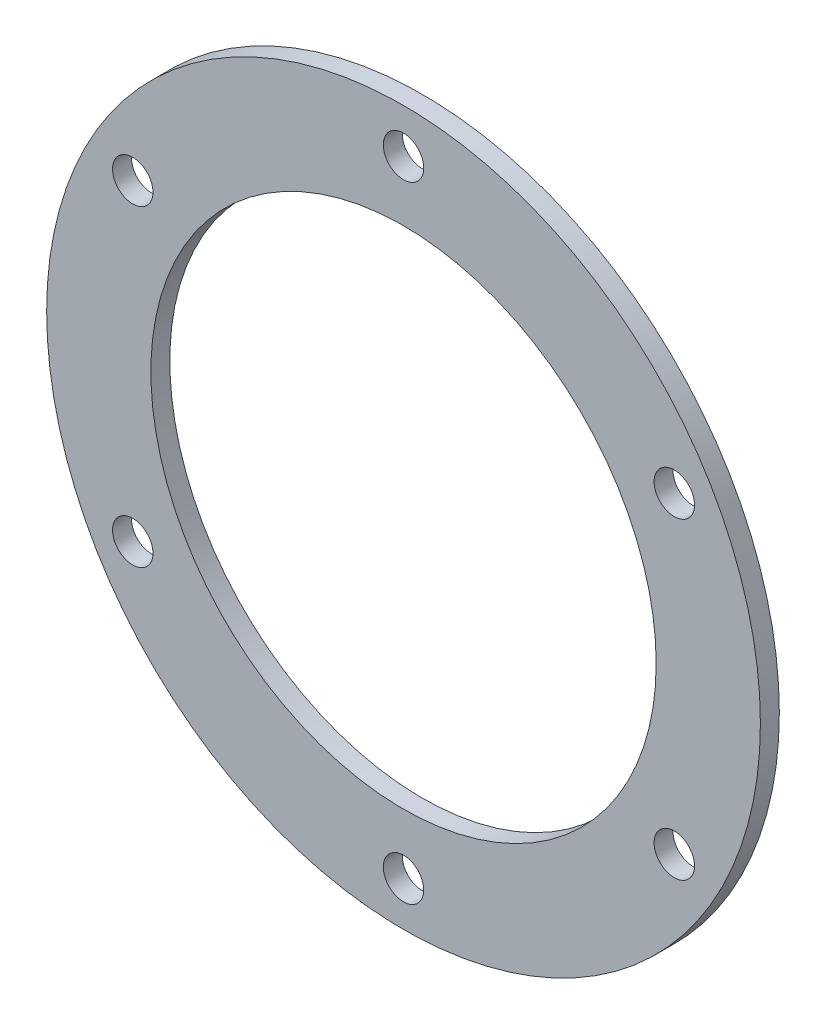
SolidWorks part; units mm, degrees
material "ABS"
ref_plane "前视基准面" through (0, 0, 0) normal (0, 0, 1) x (1, 0, 0)
ref_plane "上视基准面" through (0, 0, 0) normal (0, 1, 0) x (1, 0, 0)
ref_plane "右视基准面" through (0, 0, 0) normal (1, 0, 0) x (0, 0, -1)
sketch "草图1" plane through (0, 0, 0) normal (0, 0, 1) x (1, 0, 0)
  circle A0 centre (0, 0) radius 28.25
  circle A1 centre (0, 0) radius 20
  dimension "D1" = 56.5
  dimension "D2" = 40
extrude "凸台-拉伸1" add sketch "草图1" along normal blind 1.5
sketch "草图2" plane through (0, 0, 1.5) normal (0, 0, 1) x (1, 0, 0)
  circle A0 centre (0, 0) radius 24.75 construction
  circle A1 centre (0, 24.75) radius 1.6
  circle A2 centre (21.4341, 12.375) radius 1.6
  circle A3 centre (21.4341, -12.375) radius 1.6
  circle A4 centre (0, -24.75) radius 1.6
  circle A5 centre (-21.4341, -12.375) radius 1.6
  circle A6 centre (-21.4341, 12.375) radius 1.6
  point P5 (27.6695, 16.4344)
  point P6 (0, 0)
  point P18 (0, 0)
  dimension "D1" = 49.5
  dimension "D2" = 3.2
  dimension "D3" = 6
extrude "切除-拉伸1" cut sketch "草图2" against normal up to surface (1.5 mm away) up to face at (28.25, 0, 0)
